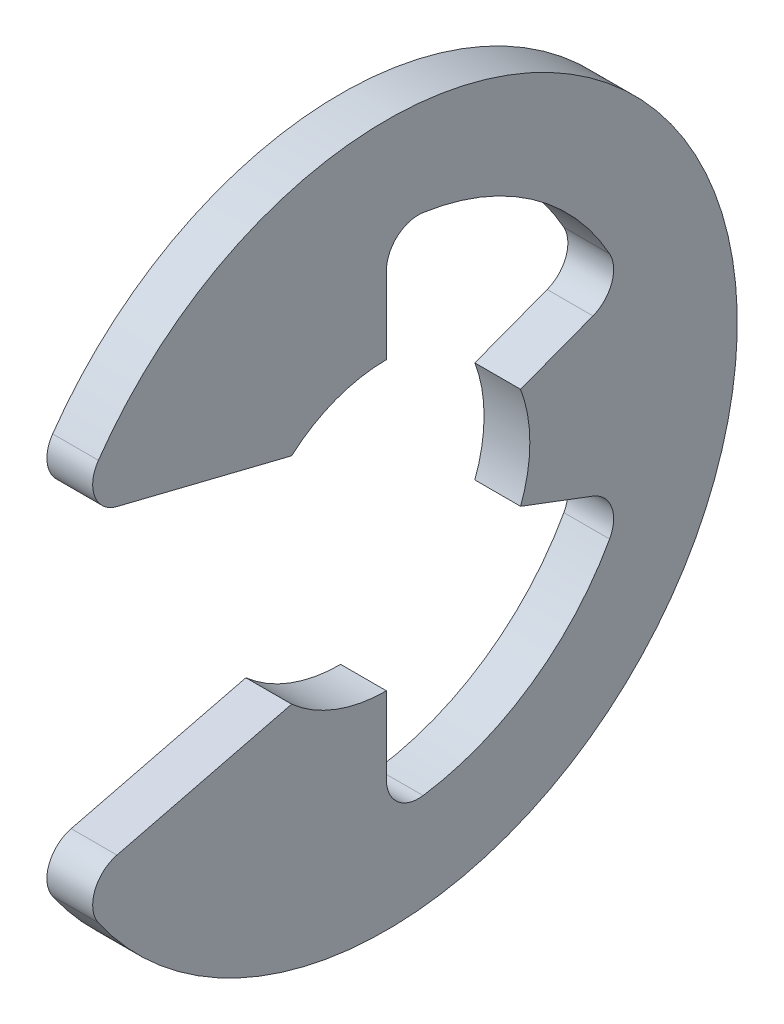
SolidWorks part; units mm, degrees
material "AISI 1020"
ref_plane "Front" through (0, 0, 0) normal (0, 0, 1) x (1, 0, 0)
ref_plane "Top" through (0, 0, 0) normal (0, 1, 0) x (1, 0, 0)
ref_plane "Right" through (0, 0, 0) normal (1, 0, 0) x (0, 0, -1)
sketch "Sketch1" plane through (0, 0, 0) normal (1, 0, 0) x (0, 0, -1)
  line L0 (-2.5938, -1.3433) -> (-0.7896, -0.8954)
  line L1 (-2.5938, 1.3433) -> (-0.7896, 0.8953)
  line L2 (0, -1.1938) -> (0, -2.1238)
  line L3 (0, 1.1938) -> (0, 2.1238)
  line L4 (1.1167, -0.4221) -> (1.9866, -0.7509)
  line L5 (1.1167, 0.4221) -> (1.9866, 0.7509)
  line L6 (0, 0) -> (-3.048, 0) construction
  line L7 (1.1167, 0.4221) -> (1.1167, -0.4221) construction
  line L8 (0, -1.1938) -> (-0.7896, -0.8954) construction
  line L9 (0, 2.921) -> (0, -2.921) construction
  circle A1 centre (0, 0) radius 3.048 construction
  circle A2 centre (0, 0) radius 1.1938 construction
  arc A3 (-2.5938, -1.3433) -> (-2.5938, 1.3433) centre (0, 0) ccw
  arc A4 (-0.7896, -0.8954) -> (0, -1.1938) centre (0, 0) ccw
  arc A5 (-0.7896, 0.8953) -> (0, 1.1938) centre (0, 0) cw
  arc A6 (1.1167, 0.4221) -> (1.1167, -0.4221) centre (0, 0) cw
  arc A7 (0, -2.1238) -> (1.9866, -0.7509) centre (0, 0) ccw
  arc A8 (1.9866, 0.7509) -> (0, 2.1238) centre (0, 0) ccw
  dimension "D1" = 2.1238
  dimension "OD" = 5.842
  dimension "L" = 6.096
  dimension "D" = 2.3876
  dimension "D2" = 1.3574
  dimension "D3" = 1.7907
extrude "Extrude1" add sketch "Sketch1" along normal mid plane 0.381
fillet "Fillet1" radius 0.2667 6 edges at (0, -2.1238, 0) (0, 2.1238, 0) (0, -1.3433, 2.5938) (0, 1.3433, 2.5938) (0, -0.7509, -1.9866) (0, 0.7509, -1.9866)
sketch "Sketch3" plane through (0, 0, 0) normal (0, 1, 0) x (1, 0, 0)
  line L0 (0.254, 1.5875) -> (0.254, 1.2065)
  line L1 (0.254, 1.2065) -> (-0.254, 1.2065)
  line L2 (-0.254, 1.2065) -> (-0.254, 1.5875)
  line L3 (-0.254, 1.5875) -> (-3.556, 1.5875)
  line L4 (1.524, 0) -> (1.524, 1.397)
  line L5 (-3.556, 1.5875) -> (-3.556, 0)
  line L6 (-3.556, 0) -> (1.524, 0)
  line L8 (1.524, 0) -> (1.524, 1.5875) construction
  line L9 (1.524, 1.5875) -> (0.254, 1.5875) construction
  line L10 (1.524, 0) -> (17.2631, 0) construction
  line L11 (1.524, 1.397) -> (1.3335, 1.5875)
  line L12 (1.3335, 1.5875) -> (0.254, 1.5875)
  point P2 (0, 1.2065)
  point P5 (0.254, 1.397)
  dimension "D1" = 1.27
  dimension "Ds" = 3.175
  dimension "Dg" = 2.413
  dimension "W" = 0.508
  dimension "D2" = 5.08
  dimension "D3" = 45
revolve "Revolve2" [suppressed] add sketch "Sketch3" angle 360 about L10
equation "\"D2@Sketch3\" = \"W@Sketch3\"*10"
equation "\"D1@Sketch3\" = \"D2@Sketch3\"/4"
equation "\"D1@Sketch1\" = (\"OD@Sketch1\"+\"D@Sketch1\")/3.875"
equation "\"D3@Sketch1\" = \"D@Sketch1\"*.75"
equation "\"D1@Fillet1\" = \"D1@Extrude1\"*.7"
